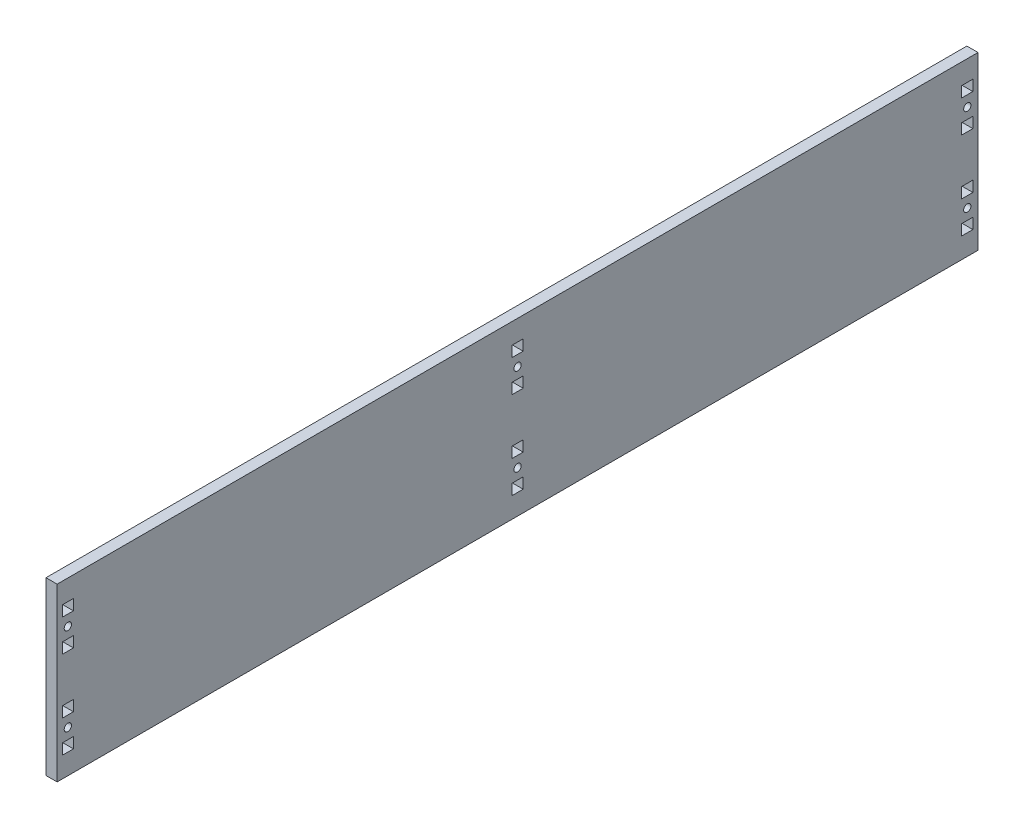
SolidWorks part; units mm, degrees
material "Acrylic (Blue)"
ref_plane "Front Plane" through (0, 0, 0) normal (0, 0, 1) x (1, 0, 0)
ref_plane "Top Plane" through (0, 0, 0) normal (0, 1, 0) x (1, 0, 0)
ref_plane "Right Plane" through (0, 0, 0) normal (1, 0, 0) x (0, 0, -1)
sketch "Sketch1" plane through (0, 0, 0) normal (1, 0, 0) x (0, 0, -1)
  line L0 (0, 0) -> (266.7, 0) construction
  line L1 (266.7, 0) -> (273.05, 0) construction
  line L2 (0, 0) -> (-266.7, 0) construction
  line L3 (-266.7, 0) -> (-273.05, 0) construction
  line L4 (-266.7, 25.9207) -> (-266.7, -25.9207) construction
  line L5 (266.7, 25.9207) -> (266.7, -25.9207) construction
  line L6 (0, 25.9207) -> (0, -25.9207) construction
  line L7 (-273.05, 50.8) -> (273.05, 50.8)
  line L8 (-273.05, 50.8) -> (-273.05, -50.8)
  line L9 (-273.05, -50.8) -> (273.05, -50.8)
  line L10 (273.05, 50.8) -> (273.05, -50.8)
  line B0 (-263.398, 19.5707) -> (-263.398, 13.2207)
  line B1 (-263.398, 13.2207) -> (-270.002, 13.2207)
  line B2 (-270.002, 13.2207) -> (-270.002, 19.5707)
  line B3 (-270.002, 19.5707) -> (-263.398, 19.5707)
  line B4 (-263.398, 38.6207) -> (-263.398, 32.2707)
  line B5 (-263.398, 32.2707) -> (-270.002, 32.2707)
  line B6 (-270.002, 32.2707) -> (-270.002, 38.6207)
  line B7 (-270.002, 38.6207) -> (-263.398, 38.6207)
  circle B8 centre (-266.7, 25.9207) radius 2.1526
  line B9 (-263.398, -32.2707) -> (-263.398, -38.6207)
  line B10 (-263.398, -38.6207) -> (-270.002, -38.6207)
  line B11 (-270.002, -38.6207) -> (-270.002, -32.2707)
  line B12 (-270.002, -32.2707) -> (-263.398, -32.2707)
  line B13 (-263.398, -13.2207) -> (-263.398, -19.5707)
  line B14 (-263.398, -19.5707) -> (-270.002, -19.5707)
  line B15 (-270.002, -19.5707) -> (-270.002, -13.2207)
  line B16 (-270.002, -13.2207) -> (-263.398, -13.2207)
  circle B17 centre (-266.7, -25.9207) radius 2.1526
  line B18 (-3.302, -19.5707) -> (-3.302, -13.2207)
  line B19 (-3.302, -13.2207) -> (3.302, -13.2207)
  line B20 (3.302, -13.2207) -> (3.302, -19.5707)
  line B21 (3.302, -19.5707) -> (-3.302, -19.5707)
  line B22 (-3.302, -38.6207) -> (-3.302, -32.2707)
  line B23 (-3.302, -32.2707) -> (3.302, -32.2707)
  line B24 (3.302, -32.2707) -> (3.302, -38.6207)
  line B25 (3.302, -38.6207) -> (-3.302, -38.6207)
  circle B26 centre (0, -25.9207) radius 2.1526
  line B27 (-3.302, 32.2707) -> (-3.302, 38.6207)
  line B28 (-3.302, 38.6207) -> (3.302, 38.6207)
  line B29 (3.302, 38.6207) -> (3.302, 32.2707)
  line B30 (3.302, 32.2707) -> (-3.302, 32.2707)
  line B31 (-3.302, 13.2207) -> (-3.302, 19.5707)
  line B32 (-3.302, 19.5707) -> (3.302, 19.5707)
  line B33 (3.302, 19.5707) -> (3.302, 13.2207)
  line B34 (3.302, 13.2207) -> (-3.302, 13.2207)
  circle B35 centre (0, 25.9207) radius 2.1526
  line B36 (263.398, -19.5707) -> (263.398, -13.2207)
  line B37 (263.398, -13.2207) -> (270.002, -13.2207)
  line B38 (270.002, -13.2207) -> (270.002, -19.5707)
  line B39 (270.002, -19.5707) -> (263.398, -19.5707)
  line B40 (263.398, -38.6207) -> (263.398, -32.2707)
  line B41 (263.398, -32.2707) -> (270.002, -32.2707)
  line B42 (270.002, -32.2707) -> (270.002, -38.6207)
  line B43 (270.002, -38.6207) -> (263.398, -38.6207)
  circle B44 centre (266.7, -25.9207) radius 2.1526
  line B45 (263.398, 32.2707) -> (263.398, 38.6207)
  line B46 (263.398, 38.6207) -> (270.002, 38.6207)
  line B47 (270.002, 38.6207) -> (270.002, 32.2707)
  line B48 (270.002, 32.2707) -> (263.398, 32.2707)
  line B49 (263.398, 13.2207) -> (263.398, 19.5707)
  line B50 (263.398, 19.5707) -> (270.002, 19.5707)
  line B51 (270.002, 19.5707) -> (270.002, 13.2207)
  line B52 (270.002, 13.2207) -> (263.398, 13.2207)
  circle B53 centre (266.7, 25.9207) radius 2.1526
  dimension "D1" = 266.7
  dimension "D2" = 101.6
  dimension "D3" = 51.8414
  dimension "D4" = 6.35
  dimension "D5" = 266.7
sketch_block_instance "BOLT_HOLE-7"
sketch_block "BOLT_HOLE" parameters "D1"=4.3053, "D2"=6.35, "D3"=6.35, "D4"=6.604
sketch_block_instance "BOLT_HOLE-8"
sketch_block_instance "BOLT_HOLE-9"
sketch_block_instance "BOLT_HOLE-10"
sketch_block_instance "BOLT_HOLE-11"
sketch_block_instance "BOLT_HOLE-12"
extrude "Boss-Extrude1" add sketch "Sketch1" along normal blind 6.604
hole_wizard "CSK for #8 Flat Head Socket Cap Screw2" positions "Sketch5" profile "Sketch4" countersink size "#8" standard "ANSI Inch" end condition through all
sketch "Sketch5" plane through (0, 0, 0) normal (-1, 0, 0) x (0, 0, 1)
  point P0 (-266.7, 25.9207)
  point P3 (-266.7, -25.9207)
  point P27 (266.7, -25.9207)
  point P30 (266.7, 25.9207)
  point P33 (0, 25.9207)
  point P36 (0, -25.9207)
sketch "Sketch4" plane through (0, 25.9207, -266.7) normal (0, 1, 0) x (0, 0, 1)
  line L0 (0, 0) -> (0, 6.604)
  line L1 (0, 6.604) -> (2.1526, 6.604)
  line L2 (2.1526, 6.604) -> (2.1526, 2.7685)
  line L3 (2.1526, 2.7685) -> (4.5593, 0)
  line L5 (4.5593, 0) -> (0, 0)
  line L6 (-2.1526, 2.7685) -> (-4.5593, 0) construction
  line L11 (0, -6.35) -> (0, 107.95) construction
  dimension "Thru Hole Dia." = 4.3053
  dimension "Thru Hole Depth" = 6.604
  dimension "Near C'Sink Dia." = 9.1186
  dimension "Near C'Sink Angle" = 82
other "Move Face1" [suppressed] parameters "D1"=0.0508
